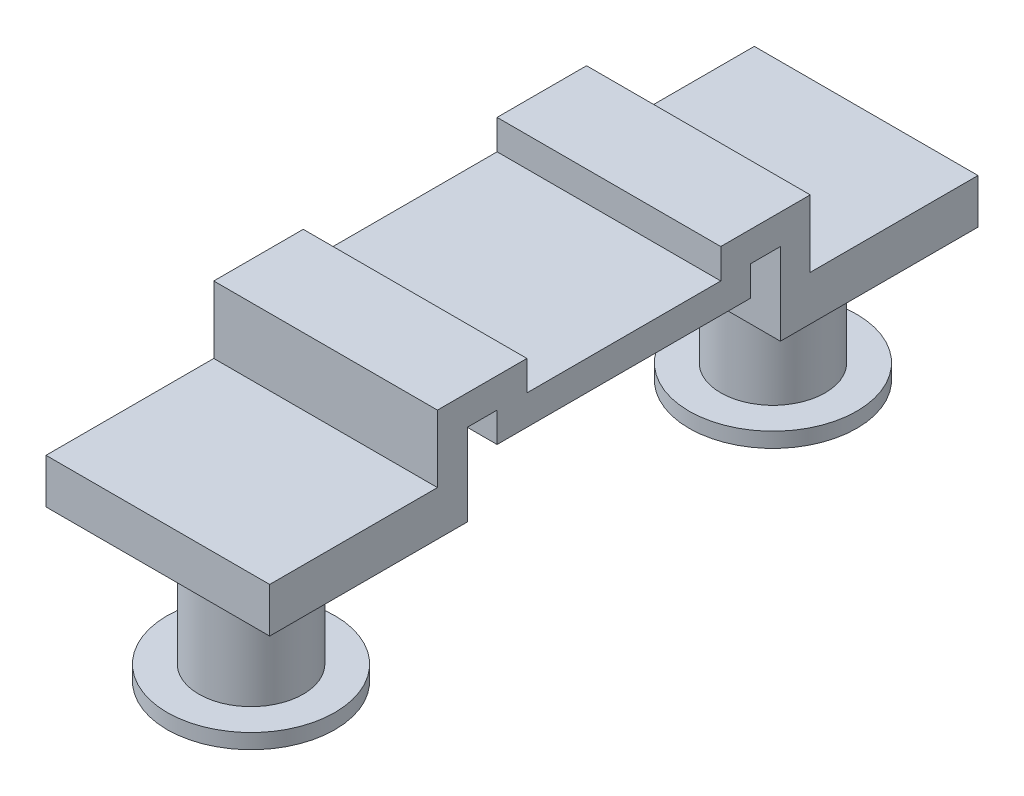
SolidWorks part; units mm, degrees
ref_plane "Front Plane" through (0, 0, 0) normal (0, 0, 1) x (1, 0, 0)
ref_plane "Top Plane" through (0, 0, 0) normal (0, 1, 0) x (1, 0, 0)
ref_plane "Right Plane" through (0, 0, 0) normal (1, 0, 0) x (0, 0, -1)
sketch "Sketch4" plane through (0, 0, 0) normal (1, 0, 0) x (0, 0, -1)
  line L20 (-5, -1) -> (-5, 0.8)
  line L21 (-5, 0.8) -> (-2.6, 0.8)
  line L22 (-2.6, 0.8) -> (-2.6, 0)
  line L29 (-4.2, 0) -> (-3.4, 0)
  line L30 (-3.4, 0) -> (-3.4, -0.8)
  line L32 (0, -0.8) -> (0, 0) construction
  line L46 (-4.2, 0) -> (-4.2, -2.2)
  line L47 (-4.2, -2.2) -> (-9.5, -2.2)
  line L48 (-9.5, -2.2) -> (-9.5, -1)
  line L49 (-9.5, -1) -> (-5, -1)
  line L51 (-2.6, 0) -> (2.6, 0)
  line L52 (-3.4, -0.8) -> (3.4, -0.8)
  line L53 (9.5, -1) -> (5, -1)
  line L54 (9.5, -2.2) -> (9.5, -1)
  line L55 (4.2, -2.2) -> (9.5, -2.2)
  line L56 (4.2, 0) -> (4.2, -2.2)
  line L57 (3.4, 0) -> (3.4, -0.8)
  line L58 (4.2, 0) -> (3.4, 0)
  line L59 (2.6, 0.8) -> (2.6, 0)
  line L60 (5, 0.8) -> (2.6, 0.8)
  line L61 (5, -1) -> (5, 0.8)
  point P19 (4.5, -2)
  point P20 (4.5, 2)
  dimension "D1" = 1.2
  dimension "D2" = 0.8
  dimension "D3" = 2.4
  dimension "D5" = 0.8
  dimension "D6" = 5.2
  dimension "D7" = 1.8
  dimension "D8" = 0.8
  dimension "D9" = 19
extrude "Boss-Extrude4" add sketch "Sketch4" along normal mid plane 6
sketch "Sketch5" plane through (0, -1, 0) normal (0, 1, 0) x (1, 0, 0)
  line L0 (-3, 0) -> (3, 0) construction
  line L1 (-3, 2.6) -> (-3, -2.6) construction
  line L2 (3, 2.6) -> (3, -2.6) construction
  circle A1 centre (0, -7) radius 1.4
  circle A2 centre (0, 7) radius 1.4
  dimension "D2" = 14
  dimension "D1" = 2.8
extrude "Boss-Extrude5" add sketch "Sketch5" against normal blind 4.6
sketch "Sketch6" plane through (0, -5.6, 0) normal (0, -1, 0) x (1, 0, 0)
  circle A0 centre (0, -7) radius 2.25
  circle A1 centre (0, 7) radius 2.25
  dimension "D1" = 4.5
extrude "Boss-Extrude6" add sketch "Sketch6" along normal blind 0.4
